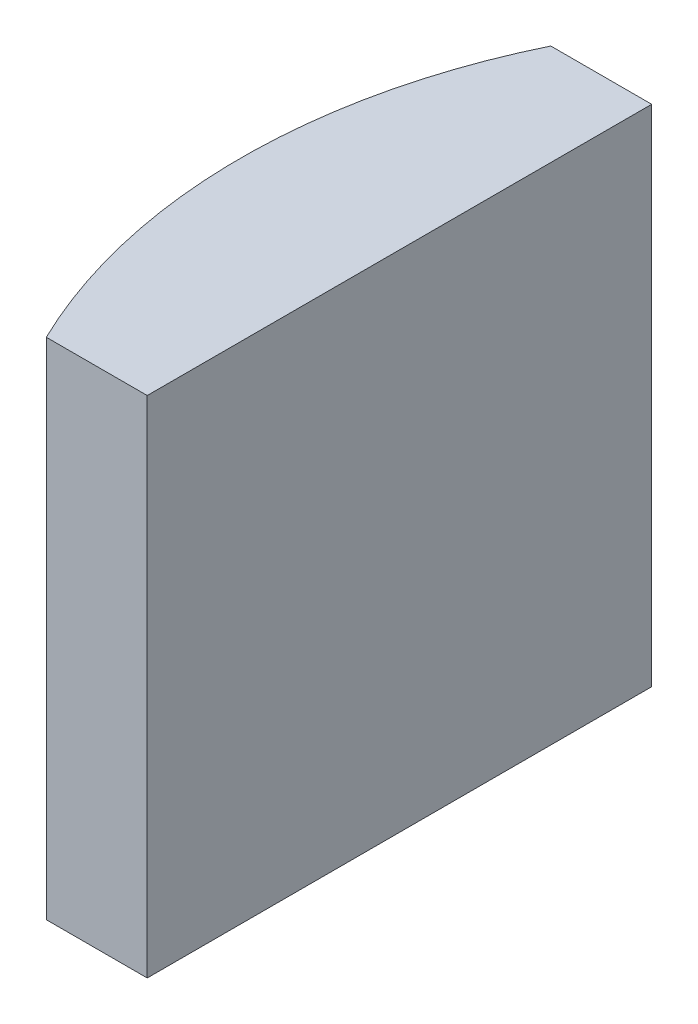
SolidWorks part; units mm, degrees
ref_plane "前视基准面" through (0, 0, 0) normal (0, 0, 1) x (1, 0, 0)
ref_plane "上视基准面" through (0, 0, 0) normal (0, 1, 0) x (1, 0, 0)
ref_plane "右视基准面" through (0, 0, 0) normal (1, 0, 0) x (0, 0, -1)
sketch "草图1" plane through (0, 0, 0) normal (0, 1, 0) x (1, 0, 0)
  line L0 (-9.3464, 0) -> (10.8051, 0) construction
  line L1 (-5.9454, 5) -> (-3.9448, 5)
  line L2 (-5.9454, -5) -> (-3.9448, -5)
  line L3 (-3.9448, 5) -> (-3.9448, -5)
  arc A0 (-5.9454, 5) -> (-5.9454, -5) centre (4.3552, 0) ccw
  point P2 (-7.0948, 0)
  point P4 (-3.9448, 0)
  point P8 (-9.3464, 0)
  dimension "D2" = 5
  dimension "D3" = 11.45
  dimension "D4" = 3.15
  dimension "D1" = 5
extrude "凸台-拉伸1" add sketch "草图1" along normal blind 10
